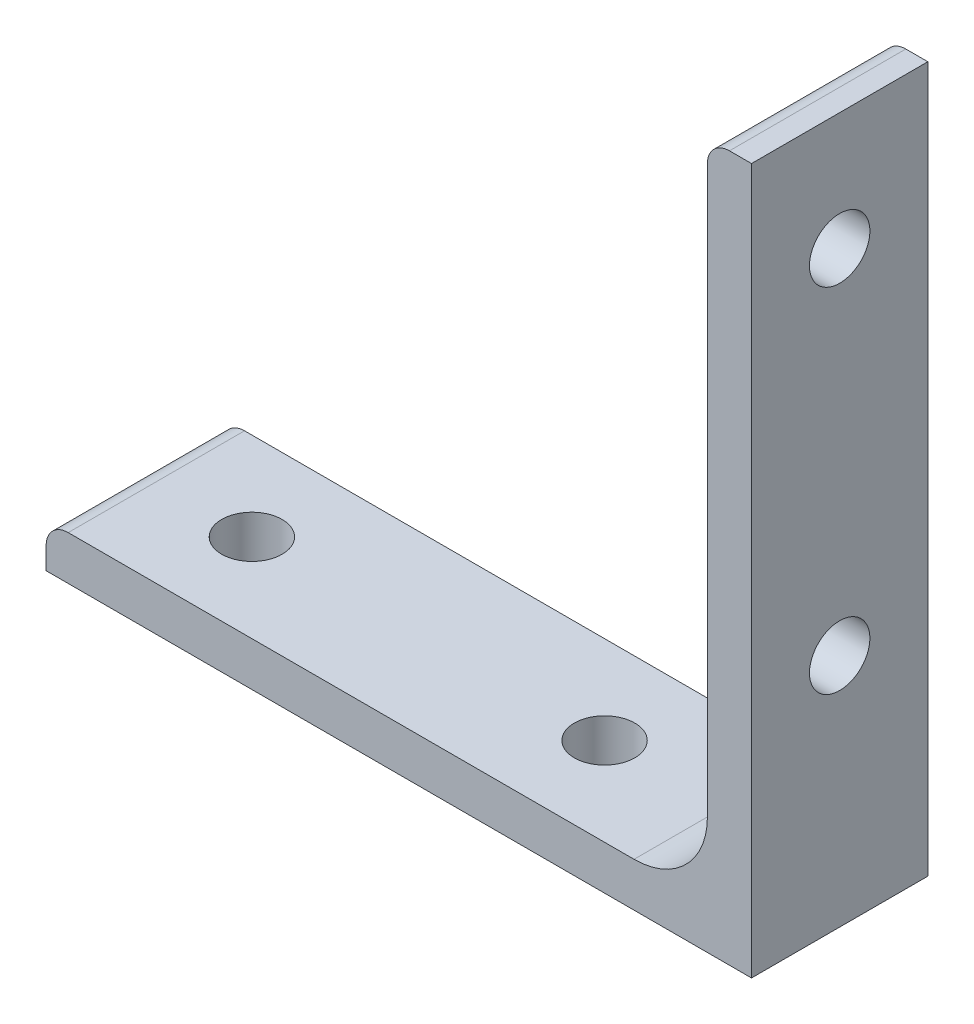
SolidWorks part; units mm, degrees
material "6061-T6 (SS)"
ref_plane "Front Plane" through (0, 0, 0) normal (0, 0, 1) x (1, 0, 0)
ref_plane "Top Plane" through (0, 0, 0) normal (0, 1, 0) x (1, 0, 0)
ref_plane "Right Plane" through (0, 0, 0) normal (1, 0, 0) x (0, 0, -1)
sketch "Sketch0" plane through (0, 0, 0) normal (0, 0, 1) x (1, 0, 0)
  line L0 (-38.1, -38.1) -> (38.1, -38.1)
  line L1 (38.1, -38.1) -> (38.1, 38.1)
  line L2 (38.1, 0) -> (0, 0) construction
  line L3 (0, 0) -> (0, -38.1) construction
  line L4 (33.3375, -25.4127) -> (33.3375, 38.1) construction
  line L5 (25.4127, -33.3375) -> (-38.1, -33.3375) construction
  arc A0 (33.3375, -25.4127) -> (25.4127, -33.3375) centre (25.4127, -25.4127) cw
  point P3 (31.0164, -31.0164)
  dimension "Inside Corner Radius" = 7.9248
  dimension "Outside Height" = 76.2
  dimension "Inside Height" = 71.4375
  dimension "Inside Width" = 71.4375
  dimension "Wall Thickness" = 4.7625
  dimension "D1" = 4.7625
  dimension "Outside Width" = 76.2
sketch "Sketch1" plane through (0, 0, 0) normal (1, 0, 0) x (0, 0, -1)
  line L0 (9.525, 0) -> (-9.525, 0)
  point P4 (0, 0)
  dimension "Length" = 19.05
sketch "Sketch2" plane through (0, 0, 0) normal (0, 0, 1) x (1, 0, 0)
  line L0 (-38.1, -38.1) -> (38.1, -38.1)
  line L1 (38.1, -38.1) -> (38.1, 38.1)
  line L2 (38.1, 38.1) -> (33.3375, 38.1) construction
  line L3 (33.3375, 35.7188) -> (33.3375, -25.4127)
  line L4 (25.4127, -33.3375) -> (-35.7187, -33.3375)
  line L5 (-38.1, -38.1) -> (-38.1, -33.3375) construction
  line L6 (35.7187, 38.1) -> (38.1, 38.1)
  line L7 (-38.1, -35.7188) -> (-38.1, -38.1)
  line L8 (38.1, 0) -> (0, 0) construction
  line L9 (0, 0) -> (0, -38.1) construction
  arc A0 (33.3375, 35.7188) -> (35.7187, 38.1) centre (35.7187, 35.7188) cw
  arc A1 (-38.1, -35.7188) -> (-35.7187, -33.3375) centre (-35.7187, -35.7188) cw
  arc A2 (33.3375, -25.4127) -> (25.4127, -33.3375) centre (25.4127, -25.4127) cw
  dimension "Inside Radius" = 7.9248
  dimension "Height" = 76.2
  dimension "Width" = 76.2
  dimension "Thickness" = 4.7625
extrude "Boss-Extrude1" add sketch "Sketch2" along normal mid plane 19.05
sketch "Break Locations" plane through (0, 0, 0) normal (1, 0, 0) x (0, 0, -1)
  line L0 (68.199, 0) -> (-68.199, 0)
  line L1 (-9.525, -38.1) -> (-9.525, 38.1) construction
  line L2 (9.525, -38.1) -> (9.525, 38.1) construction
  point P0 (55.245, 0)
  point P1 (-55.245, 0)
  point P10 (0, 0)
  point P11 (-68.199, 0)
  point P13 (68.199, 0)
  dimension "D1" = 64.77
  dimension "D2" = 64.77
  dimension "D3" = 77.724
ref_plane "Plane1" through (0, 0, 0) normal (0.7071, 0.7071, 0) x (0.7071, -0.7071, 0)
hole_wizard "F (0.257) Diameter Hole1" positions "Sketch5" profile "Sketch6" hole size "F" standard "ANSI Inch" end condition through all
sketch "Sketch5" plane through (0, -33.3375, 0) normal (0, 1, 0) x (1, 0, 0)
  line L0 (-35.7187, 0) -> (25.4127, 0) construction
  line L1 (-35.7187, -9.525) -> (-35.7187, 9.525) construction
  line L2 (25.4127, -9.525) -> (25.4127, 9.525) construction
  line L4 (38.1, -9.525) -> (38.1, 9.525) construction
  line L5 (38.1, -9.525) -> (38.1, 9.525) construction
  point P0 (12.7, 0)
  point P2 (-25.4, 0)
  point P13 (0, 0)
  point P14 (0, 0)
  dimension "D1" = 63.5
  dimension "D2" = 25.4
sketch "Sketch6" plane through (12.7, -33.3375, 0) normal (1, 0, 0) x (0, 0, 1)
  line L0 (0, 0) -> (0, 4.7625)
  line L1 (0, 4.7625) -> (3.2639, 4.7625)
  line L2 (3.2639, 4.7625) -> (3.2639, 0)
  line L5 (3.2639, 0) -> (0, 0)
  line L11 (0, -6.35) -> (0, 107.95) construction
  dimension "Thru Hole Dia." = 6.5278
  dimension "Thru Hole Depth" = 4.7625
mirror "Mirror1" about plane through (0, 0, 0) normal (0.7071, 0.7071, 0) of "F (0.257) Diameter Hole1"
equation "\"D1@Break Locations\" = .85 * \"Height@Sketch2\""
equation "\"D2@Break Locations\"=\"D1@Break Locations\""
equation "\"Thickness@Sketch2\"=\"wall thickness@sketch0\""
equation "\"Height@Sketch2\"=\"outside height@sketch0\""
equation "\"Width@Sketch2\"=\"outside width@sketch0\""
equation "\"Inside Radius@Sketch2\"=\"inside corner radius@sketch0\""
equation "\"Length@Boss-Extrude1\"=\"length@sketch1\""
equation "\"D3@Break Locations\"=\"D2@Break Locations\"*1.2"
equation "\"D1@Sketch0\"=\"Wall Thickness@Sketch0\""
